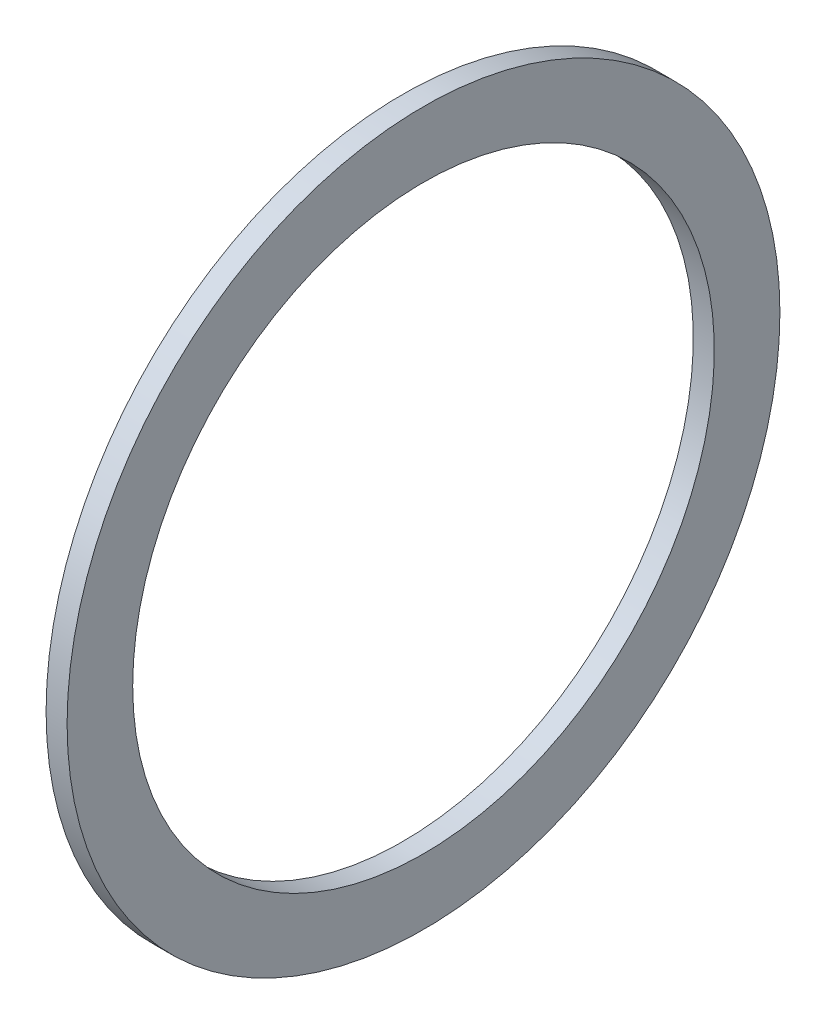
SolidWorks part; units mm, degrees
ref_plane "Front Plane" through (0, 0, 0) normal (0, 0, 1) x (1, 0, 0)
ref_plane "Top Plane" through (0, 0, 0) normal (0, 1, 0) x (1, 0, 0)
ref_plane "Right Plane" through (0, 0, 0) normal (1, 0, 0) x (0, 0, -1)
sketch "Sketch2" plane through (0, 0, 0) normal (0, 0, 1) x (1, 0, 0)
  line L0 (0, 0) -> (58.591, 0) construction
  line L2 (0, 0) -> (18.4, 0)
  line L3 (0, 0) -> (0, 2.5)
  line L4 (0, 2.5) -> (18.4, 2.5)
  line L5 (18.4, 0) -> (18.4, 2.5)
  line L6 (6.0094, 2.5) -> (6.0094, 6)
  line L11 (6.0094, 6) -> (9.9794, 6)
  line L16 (12.9794, 6) -> (12.9794, 3)
  line L17 (12.9794, 3) -> (13.6398, 3)
  line L18 (13.6398, 3) -> (13.6398, 2.5)
  line L19 (13.6398, 2.5) -> (6.0094, 2.5)
  line L22 (13.6398, 2.5) -> (16.1198, 2.5)
  line L23 (13.6398, 2.5) -> (13.6398, 4)
  line L24 (13.6398, 4) -> (16.1198, 4)
  line L25 (16.1198, 2.5) -> (16.1198, 4)
  line L27 (6.0094, 6) -> (9.9794, 6)
  line L28 (6.0094, 6) -> (6.0094, 9)
  line L29 (6.0094, 9) -> (9.9794, 9)
  line L30 (9.9794, 6) -> (9.9794, 9)
  line L31 (6.0094, 9) -> (6.0094, 8.25)
  line L32 (6.0094, 8.25) -> (5.0094, 8.25)
  line L33 (8.6609, 22.001) -> (8.6609, 12.476) construction
  line L34 (5.0094, 12.476) -> (12.3124, 12.476)
  line L35 (9.9794, 9) -> (12.3124, 9)
  line L36 (5.0094, 7.9375) -> (1.7709, 7.9375)
  line L37 (5.0094, 8.25) -> (5.0094, 12.476)
  line L38 (5.0094, 7.9375) -> (5.0094, 13.9365)
  line L39 (5.0094, 13.9365) -> (1.7709, 13.9365)
  line L40 (1.7709, 7.9375) -> (1.7709, 13.9365)
  line L41 (5.0094, 22.001) -> (12.3124, 22.001)
  line L42 (5.0094, 22.001) -> (5.0094, 30.1625)
  line L43 (5.0094, 30.1625) -> (12.3124, 30.1625)
  line L44 (12.3124, 22.001) -> (12.3124, 30.1625)
  line L49 (16.6398, 22.001) -> (16.6398, 7.5)
  line L51 (23.0198, 7.5) -> (23.0198, 6.5)
  line L54 (16.1198, 4) -> (13.6398, 4)
  line L56 (18.0398, 7.5) -> (23.0198, 7.5)
  line L57 (13.3124, 22.001) -> (16.6398, 22.001)
  line L58 (16.1198, 3.5) -> (20.0198, 3.5)
  line L59 (29.9098, 14) -> (26.9098, 11)
  line L60 (4.0094, 31.75) -> (18.0398, 31.75)
  line L61 (18.0398, 7.5) -> (23.0198, 7.5)
  line L62 (18.0398, 7.5) -> (18.0398, 12)
  line L63 (18.0398, 12) -> (23.0198, 12)
  line L64 (23.0198, 7.5) -> (23.0198, 12)
  line L65 (18.0398, 31.75) -> (18.0398, 12)
  line L66 (23.0198, 11) -> (26.9098, 11)
  line L67 (34.8098, 23) -> (31.3098, 19.5)
  line L68 (35.8098, 31) -> (38.7998, 33.99)
  line L69 (29.9098, 14) -> (29.9098, 15)
  line L70 (29.9098, 15) -> (22.9398, 15)
  line L71 (22.9398, 15) -> (21.0398, 15)
  line L72 (18.0398, 7.5) -> (16.6398, 7.5)
  line L73 (21.0398, 15) -> (21.0398, 43)
  line L74 (19.6115, 40) -> (9.6516, 40)
  line L75 (9.6516, 40) -> (4.0094, 40)
  line L76 (21.0398, 43) -> (19.6115, 43)
  line L77 (22.9398, 15) -> (29.9098, 15)
  line L78 (22.9398, 15) -> (22.9398, 21)
  line L79 (22.9398, 21) -> (29.9098, 21)
  line L80 (29.9098, 15) -> (29.9098, 21)
  line L81 (9.6516, 40) -> (19.6115, 40)
  line L82 (9.6516, 40) -> (9.6516, 50)
  line L83 (9.6516, 50) -> (19.6115, 50)
  line L84 (19.6115, 40) -> (19.6115, 50)
  line L85 (4.0094, 40) -> (4.0094, 31.75)
  line L86 (12.9794, 3) -> (12.9794, 2.5)
  line L87 (31.3098, 19.5) -> (29.9098, 19.5)
  line L88 (21.4694, 63.5) -> (21.4694, 51.308)
  line L89 (21.4694, 63.5) -> (25.9398, 63.5)
  line L90 (25.9398, 63.5) -> (25.9398, 25)
  line L91 (27.8398, 25) -> (25.9398, 25)
  line L92 (9.6516, 48) -> (8.2233, 48)
  line L93 (8.2233, 48) -> (8.2233, 53.476)
  line L94 (8.2233, 53.476) -> (19.6115, 53.476)
  line L95 (19.6115, 53.476) -> (19.6115, 50)
  line L96 (13.9174, 63.001) -> (13.9174, 53.476) construction
  line L97 (8.2233, 63.001) -> (19.6115, 63.001)
  line L98 (8.2233, 63.001) -> (8.2233, 68.2625)
  line L99 (8.2233, 68.2625) -> (19.6115, 68.2625)
  line L100 (19.6115, 63.001) -> (19.6115, 68.2625)
  line L101 (12.9794, 6) -> (11.9794, 6)
  line L102 (8.2233, 44.825) -> (4.9848, 44.825)
  line L103 (8.2233, 44.825) -> (8.2233, 54.9365)
  line L104 (8.2233, 54.9365) -> (4.9848, 54.9365)
  line L106 (9.9794, 6) -> (10.8794, 6)
  line L107 (27.8398, 25) -> (34.8098, 25)
  line L108 (34.8098, 25) -> (34.8098, 23)
  line L109 (0, 0) -> (-2, 0)
  line L110 (0, 0) -> (0, 11)
  line L111 (27.8398, 25) -> (34.8098, 25)
  line L112 (27.8398, 25) -> (27.8398, 32.5)
  line L113 (27.8398, 32.5) -> (34.8098, 32.5)
  line L114 (34.8098, 25) -> (34.8098, 32.5)
  line L115 (35.8098, 31) -> (34.8098, 31)
  line L116 (27.8398, 32.5) -> (27.8398, 64.5)
  line L117 (20.5849, 74.025) -> (6.2499, 74.025)
  line L118 (6.2499, 74.025) -> (6.2499, 76.2)
  line L119 (38.7998, 47.29) -> (30.8398, 55.25)
  line L120 (0, 11) -> (-2, 11)
  line L121 (38.7998, 43.815) -> (30.8623, 43.815)
  line L123 (-4.8152, 69.85) -> (1.5348, 76.2)
  line L124 (38.7998, 47.29) -> (38.7998, 33.99)
  line L125 (-2, 0) -> (-2, 11)
  line L126 (38.7998, 37.465) -> (30.8623, 37.465)
  line L127 (30.8623, 43.815) -> (30.8623, 37.465)
  line L128 (6.0094, 2.5) -> (6.0094, 0)
  line L129 (-0.0152, 63.5) -> (-0.0152, 30)
  line L132 (4.9848, 63.5) -> (-0.0152, 63.5)
  line L136 (-1.8152, 30) -> (-11.7752, 30)
  line L138 (-13.7752, 25.4) -> (-2, 25.4)
  line L139 (-2, 25.4) -> (-2, 11.5)
  line L140 (27.8398, 64.5) -> (20.5849, 64.5)
  line L141 (-1.8152, 30) -> (-11.7752, 30)
  line L142 (-1.8152, 30) -> (-1.8152, 39)
  line L143 (-1.8152, 39) -> (-11.7752, 39)
  line L144 (-11.7752, 30) -> (-11.7752, 39)
  line L145 (20.5849, 64.5) -> (20.5849, 74.025)
  line L146 (-12.7752, 37) -> (-12.7752, 47.29)
  line L147 (-12.7752, 37) -> (-11.7752, 37)
  line L148 (30.8398, 55.25) -> (30.8398, 76.2)
  line L149 (11.9794, 6) -> (11.9794, 5.45)
  line L154 (-2, 11.5) -> (0.5, 11.5)
  line L155 (4.9848, 60.6197) -> (24.0348, 60.6197)
  line L160 (4.9848, 60.6197) -> (4.9848, 55.8572)
  line L161 (4.9848, 55.8572) -> (24.0348, 55.8572)
  line L166 (24.0348, 60.6197) -> (24.0348, 55.8572)
  line L167 (4.9848, 60.6197) -> (24.0348, 55.8572) construction
  line L172 (4.9848, 55.8572) -> (24.0348, 60.6197) construction
  line L173 (24.0348, 62.2072) -> (25.9398, 62.2072)
  line L174 (11.9794, 5.45) -> (10.8794, 5.45)
  line L175 (10.8794, 6) -> (10.8794, 5.45)
  line L176 (24.0348, 62.2072) -> (24.0348, 54.2697)
  line L177 (24.0348, 54.2697) -> (25.9398, 54.2697)
  line L178 (25.9398, 62.2072) -> (25.9398, 54.2697)
  line L179 (24.0348, 62.2072) -> (25.9398, 54.2697) construction
  line L180 (24.0348, 54.2697) -> (25.9398, 62.2072) construction
  line L181 (3, 19.6197) -> (15.7, 19.6197)
  line L182 (3, 19.6197) -> (3, 14.8572)
  line L183 (3, 14.8572) -> (15.7, 14.8572)
  line L184 (15.7, 19.6197) -> (15.7, 14.8572)
  line L185 (3, 19.6197) -> (15.7, 14.8572) construction
  line L186 (3, 14.8572) -> (15.7, 19.6197) construction
  line L187 (15.7, 21.2072) -> (16.6398, 21.2072)
  line L188 (15.7, 21.2072) -> (15.7, 13.2697)
  line L189 (15.7, 13.2697) -> (16.6398, 13.2697)
  line L190 (16.6398, 21.2072) -> (16.6398, 13.2697)
  line L191 (15.7, 21.2072) -> (16.6398, 13.2697) construction
  line L192 (15.7, 13.2697) -> (16.6398, 21.2072) construction
  line L193 (0.5, 11.5) -> (0.5, 6.9375)
  line L194 (0.5, 6.9375) -> (1.7709, 6.9375)
  line L195 (23.0198, 6.5) -> (20.0198, 3.5)
  line L196 (4.9848, 63.5) -> (4.9848, 54.9365)
  line L197 (3, 43.825) -> (4.9848, 43.825)
  line L198 (1.7709, 6.9375) -> (1.7709, 7.9375)
  line L199 (6.0094, 0) -> (12.9794, 0)
  line L200 (12.9794, 0) -> (12.9794, 2.5)
  line L201 (18.0398, 31.75) -> (18.0398, 35.875)
  line L202 (18.0398, 35.875) -> (21.0398, 35.875)
  line L203 (30.8398, 76.2) -> (6.2499, 76.2)
  line L204 (2.8049, 69.85) -> (7.2499, 69.85) construction
  line L205 (7.2499, 67.4688) -> (26.2999, 67.4688)
  line L206 (7.2499, 74.025) -> (7.2499, 64.5)
  line L207 (7.2499, 64.5) -> (-1.8152, 64.5)
  line L208 (-1.8152, 64.5) -> (-1.8152, 39)
  line L209 (-12.7752, 47.29) -> (-4.8152, 55.25)
  line L210 (-4.8152, 55.25) -> (-4.8152, 69.85)
  line L211 (7.2499, 67.4688) -> (7.2499, 72.2312)
  line L212 (7.2499, 72.2312) -> (26.2999, 72.2313)
  line L213 (26.2999, 67.4688) -> (26.2999, 72.2313)
  line L214 (26.2999, 73.8187) -> (30.8398, 73.8187)
  line L215 (26.2999, 73.8187) -> (26.2999, 65.8813)
  line L216 (26.2999, 65.8813) -> (30.8398, 65.8813)
  line L217 (30.8398, 73.8187) -> (30.8398, 65.8813)
  line L218 (2.8049, 72.2313) -> (25.0299, 72.2313)
  line L219 (2.8049, 72.2313) -> (2.8049, 67.4687)
  line L220 (2.8049, 67.4687) -> (25.0299, 67.4687)
  line L221 (25.0299, 72.2313) -> (25.0299, 67.4687)
  line L222 (25.0299, 69.85) -> (20.5849, 69.85) construction
  line L223 (21.4694, 51.308) -> (22.9398, 51.308)
  line L224 (22.9398, 51.308) -> (22.9398, 21)
  line L225 (13.6398, 4) -> (13.6398, 12.2697)
  line L226 (13.6398, 12.2697) -> (13.3124, 12.2697)
  line L227 (13.3124, 12.2697) -> (13.3124, 22.001)
  line L228 (12.3124, 9) -> (12.3124, 12.476)
  line L229 (-1.8152, 30) -> (-0.0152, 30)
  line L230 (8.2233, 65.6317) -> (2.8049, 65.6317) construction
  line L231 (19.6115, 65.6317) -> (25.0299, 65.6317) construction
  line L232 (1.5348, 76.2) -> (6.2499, 76.2)
  line L233 (-11.7752, 30) -> (-13.7752, 30)
  line L234 (-13.7752, 30) -> (-13.7752, 25.4)
  line L235 (3, 13.9365) -> (3, 43.825)
  line L236 (4.9848, 54.9365) -> (4.9848, 44.825)
  line L237 (4.9848, 43.825) -> (4.9848, 44.825)
  circle A0 centre (26.8898, 25.95) radius 0.95
  circle A1 centre (21.9898, 15.95) radius 0.95
  circle A2 centre (17.3398, 8.2) radius 0.7
  circle A3 centre (10.4294, 6.45) radius 0.45
  circle A4 centre (-0.9152, 30.9) radius 0.9
  point P7 (24.9873, 58.2385)
  point P131 (16.1699, 17.2385)
  point P135 (14.5098, 58.2385)
  point P146 (9.35, 17.2385)
sketch "Sketch3" plane through (0, 0, 0) normal (0, 0, 1) x (1, 0, 0)
  line L0 (8.2233, 44.825) -> (8.2233, 54.9365) construction
  line L1 (8.2233, 54.9365) -> (4.9848, 54.9365) construction
  line L3 (8.2233, 44.825) -> (4.9848, 44.825) construction
  line L4 (8.2233, 44.825) -> (8.2233, 54.9365)
  line L5 (8.2233, 54.9365) -> (4.9848, 54.9365)
  line L7 (8.2233, 44.825) -> (4.9848, 44.825)
  line L8 (4.9848, 54.9365) -> (4.9848, 44.825) construction
  line L9 (4.9848, 54.9365) -> (4.9848, 44.825)
revolve "Revolve1" add sketch "Sketch3" angle 360 about L0
